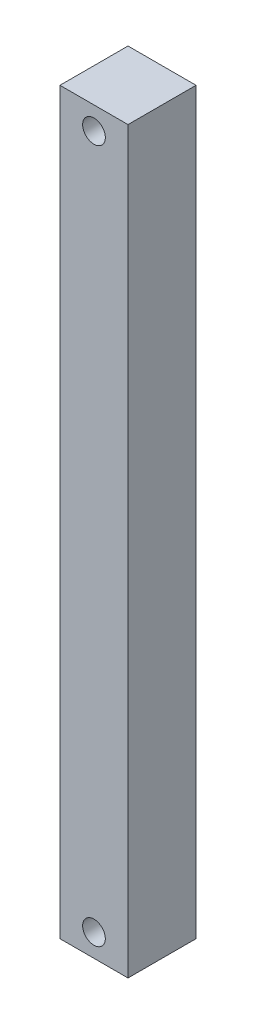
SolidWorks part; units mm, degrees
ref_plane "Front Plane" through (0, 0, 0) normal (0, 0, 1) x (1, 0, 0)
ref_plane "Top Plane" through (0, 0, 0) normal (0, 1, 0) x (1, 0, 0)
ref_plane "Right Plane" through (0, 0, 0) normal (1, 0, 0) x (0, 0, -1)
sketch "Sketch1" plane through (0, 0, 0) normal (0, 1, 0) x (1, 0, 0)
  line L1 (-1.5, 1.5) -> (1.5, 1.5)
  line L2 (-1.5, 1.5) -> (-1.5, -1.5)
  line L3 (-1.5, -1.5) -> (1.5, -1.5)
  line L4 (1.5, 1.5) -> (1.5, -1.5)
  line L5 (-1.5, 1.5) -> (1.5, -1.5) construction
  line L6 (-1.5, -1.5) -> (1.5, 1.5) construction
  point P0 (0, 0)
  dimension "D1" = 3
  dimension "D2" = 3
extrude "Boss-Extrude1" add sketch "Sketch1" along normal blind 32.59
sketch "Sketch2" plane through (0, 0, 1.5) normal (0, 0, 1) x (1, 0, 0)
  line L0 (0, 0) -> (0, 2.3948) construction
  line L1 (-1.5, 0) -> (1.5, 0) construction
  circle A0 centre (0, 1) radius 0.5
  dimension "D1" = 1
  dimension "D2" = 1
extrude "Cut-Extrude1" cut sketch "Sketch2" against normal through all
sketch "Sketch3" plane through (0, 0, 1.5) normal (0, 0, 1) x (1, 0, 0)
  line L0 (-1.5, 32.59) -> (1.5, 32.59) construction
  line L1 (0, 0) -> (0, 45.5351) construction
  line L2 (-1.5, 0) -> (1.5, 0) construction
  circle A0 centre (0, 31.59) radius 0.5007
  dimension "D1" = 1.0014
  dimension "D2" = 1
extrude "Cut-Extrude2" cut sketch "Sketch3" against normal up to next
